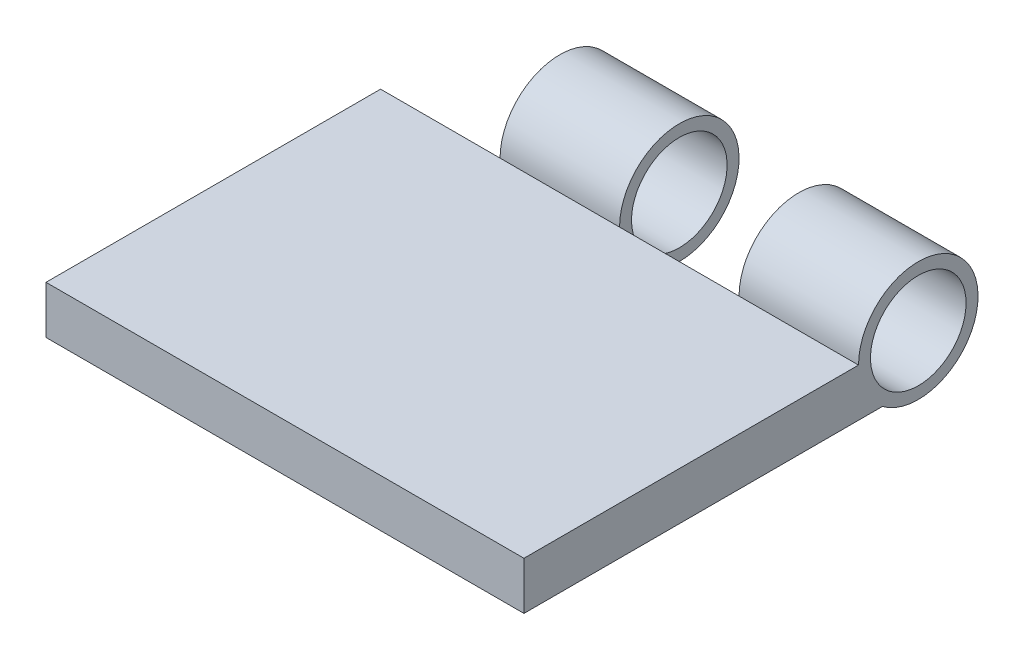
SolidWorks part; units mm, degrees
ref_plane "Front Plane" through (0, 0, 0) normal (0, 0, 1) x (1, 0, 0)
ref_plane "Top Plane" through (0, 0, 0) normal (0, 1, 0) x (1, 0, 0)
ref_plane "Right Plane" through (0, 0, 0) normal (1, 0, 0) x (0, 0, -1)
sketch "Sketch2" plane through (0, 0, 0) normal (0, 1, 0) x (1, 0, 0)
  line L1 (-10, -7) -> (10, -7)
  line L2 (-10, -7) -> (-10, 7)
  line L3 (-10, 7) -> (10, 7)
  line L4 (10, -7) -> (10, 7)
  line L5 (-10, -7) -> (10, 7) construction
  line L6 (-10, 7) -> (10, -7) construction
  point P0 (0, 0)
  dimension "D1" = 14
  dimension "D2" = 20
extrude "Boss-Extrude2" add sketch "Sketch2" along normal blind 2
sketch "Sketch3" plane through (10, 0, 0) normal (1, 0, 0) x (0, 0, -1)
  line L0 (7, 2) -> (12, 2)
  line L1 (7, 0) -> (8, 0)
  arc A0 (8, 0) -> (7, 2) centre (9.5, 2) ccw
  line M2 (7, 0) -> (7, 2)
  dimension "D1" = 5
extrude "Boss-Extrude3" add sketch "Sketch3" against normal blind 5 contours L1 A0 L0 M2 | L0 A0
ref_plane "Plane1" through (2.5, 0, 0) normal (-1, 0, 0) x (0, 0, 1)
mirror "Mirror1" about plane through (2.5, 0, 0) normal (-1, 0, 0) of "Boss-Extrude3"
sketch "Sketch4" plane through (10, 0, 0) normal (1, 0, 0) x (0, 0, -1)
  circle A0 centre (9.5, 2) radius 2
  dimension "D1" = 4
extrude "Cut-Extrude1" cut sketch "Sketch4" against normal through all
